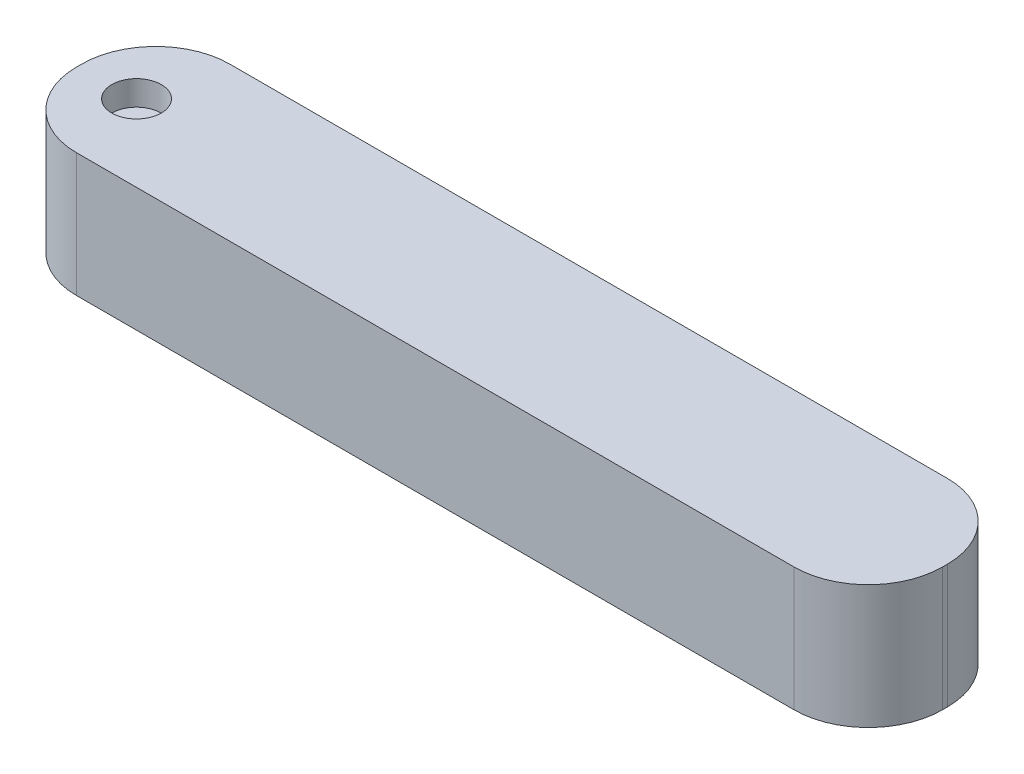
SolidWorks part; units mm, degrees
ref_plane "Front Plane" through (0, 0, 0) normal (0, 0, 1) x (1, 0, 0)
ref_plane "Top Plane" through (0, 0, 0) normal (0, 1, 0) x (1, 0, 0)
ref_plane "Right Plane" through (0, 0, 0) normal (1, 0, 0) x (0, 0, -1)
sketch "Sketch1" plane through (0, 0, 0) normal (0, 1, 0) x (1, 0, 0)
  line L1 (-32.3318, 11.1125) -> (56.5682, 11.1125)
  line L2 (-32.3318, 11.1125) -> (-32.3318, -4.6355)
  line L3 (-32.3318, -4.6355) -> (56.5682, -4.6355)
  line L4 (56.5682, 11.1125) -> (56.5682, -4.6355)
  dimension "D1" = 88.9
  dimension "D2" = 15.748
extrude "Boss-Extrude1" add sketch "Sketch1" along normal blind 12.7
fillet "Fillet1" radius 7.62 4 edges at (-32.3318, 6.35, -11.1125) (-32.3318, 6.35, 4.6355) (56.5682, 6.35, -11.1125) (56.5682, 6.35, 4.6355)
sketch "Sketch2" plane through (0, 12.7, 0) normal (0, 1, 0) x (1, 0, 0)
  circle A0 centre (-26.4287, 3.2385) radius 2.54
  dimension "D1" = 5.08
extrude "Cut-Extrude1" cut sketch "Sketch2" against normal blind 2.54
sketch "Sketch3" plane through (0, 0, 0) normal (0, -1, 0) x (1, 0, 0)
  circle A0 centre (-26.4287, -3.2385) radius 2.54
  circle A1 centre (-26.4287, -3.2385) radius 2.54 construction
  dimension "D1" = 0
extrude "Cut-Extrude2" cut sketch "Sketch3" against normal blind 7.62
sketch "Sketch4" plane through (0, 10.16, 0) normal (0, 1, 0) x (1, 0, 0)
  circle A0 centre (-26.4287, 3.2385) radius 1.016
  dimension "D1" = 2.032
extrude "Cut-Extrude3" cut sketch "Sketch4" against normal blind 5.08
